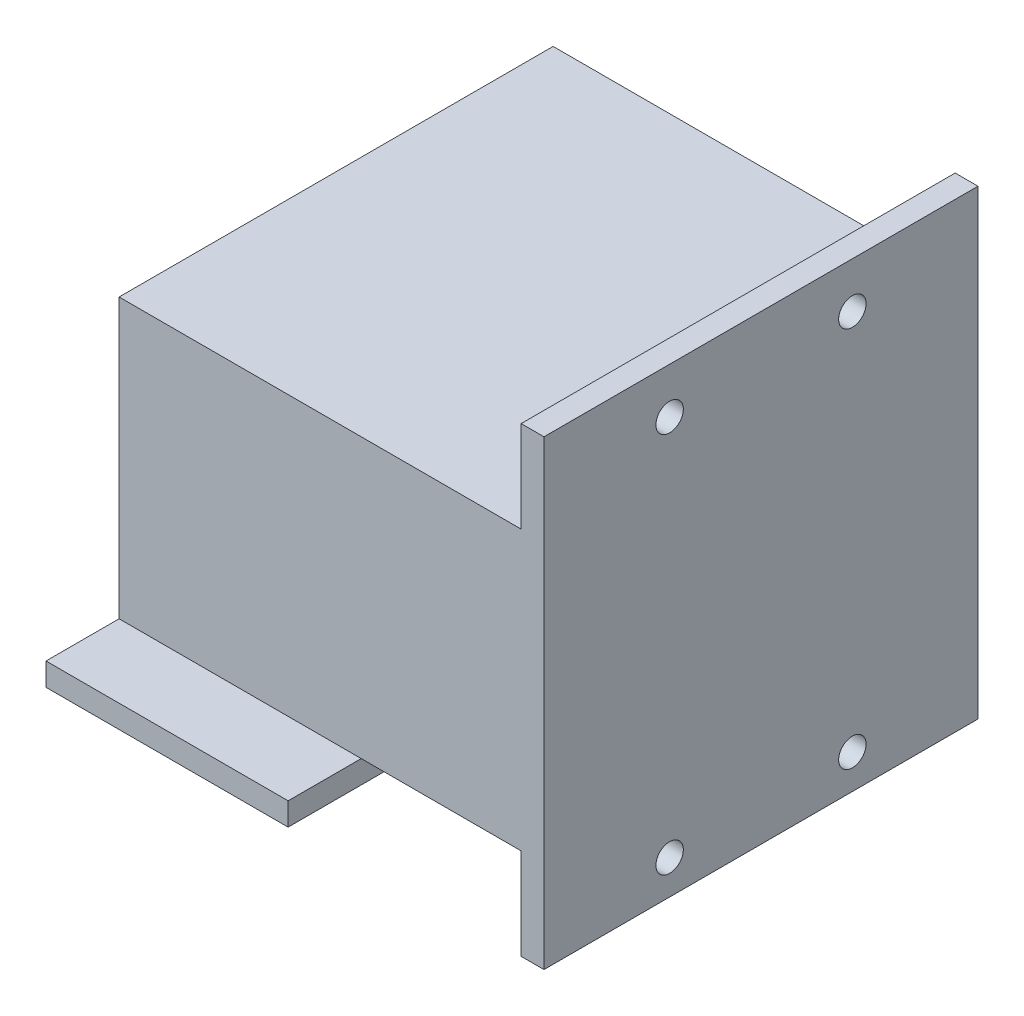
SolidWorks part; units mm, degrees
ref_plane "Front Plane" through (0, 0, 0) normal (0, 0, 1) x (1, 0, 0)
ref_plane "Top Plane" through (0, 0, 0) normal (0, 1, 0) x (1, 0, 0)
ref_plane "Right Plane" through (0, 0, 0) normal (1, 0, 0) x (0, 0, -1)
sketch "Sketch1" plane through (0, 0, 0) normal (0, 1, 0) x (1, 0, 0)
  line L0 (-9.7936, -23.704) -> (11.7064, -23.704)
  line L1 (-9.7936, -23.704) -> (-9.7936, 18.796)
  line L2 (-9.7936, 18.796) -> (11.7064, 18.796)
  line L3 (11.7064, -23.704) -> (11.7064, 18.796)
  line L5 (-12.2936, 21.296) -> (14.2064, 21.296)
  line L6 (-12.2936, 21.296) -> (-12.2936, -26.204)
  line L7 (-12.2936, -26.204) -> (14.2064, -26.204)
  line L8 (14.2064, 21.296) -> (14.2064, -26.204)
  dimension "D1" = 21.5
  dimension "D2" = 42.5
  dimension "D3" = 2.5
  dimension "D4" = 2.5
  dimension "D5" = 2.5
  dimension "D6" = 2.5
extrude "Boss-Extrude1" add sketch "Sketch1" along normal blind 33
sketch "Sketch2" plane through (0, 33, 0) normal (0, 1, 0) x (1, 0, 0)
  line L1 (-9.7936, 18.796) -> (11.7064, 18.796)
  line L2 (-9.7936, 18.796) -> (-9.7936, -23.704)
  line L3 (-9.7936, -23.704) -> (11.7064, -23.704)
  line L4 (11.7064, 18.796) -> (11.7064, -23.704)
extrude "Boss-Extrude2" add sketch "Sketch2" against normal blind 2.5
sketch "Sketch3" plane through (0, 0, -21.296) normal (0, 0, -1) x (-1, 0, 0)
  line L0 (-0.9564, 33) -> (-0.9564, 0) construction
  line L1 (-14.2064, 33) -> (12.2936, 33) construction
  line L2 (-14.2064, 0) -> (12.2936, 0) construction
  line L3 (2.5436, 30.5) -> (2.5436, 0)
  line L4 (2.5436, 0) -> (-0.9564, 0)
  line L5 (-0.9564, 0) -> (-4.4564, 0)
  line L6 (-4.4564, 0) -> (-4.4564, 30.5)
  line L9 (-4.4564, 30.5) -> (2.5436, 30.5)
  dimension "D1" = 3.5
  dimension "D2" = 3.5
  dimension "D3" = 2.5
extrude "Cut-Extrude2" cut sketch "Sketch3" against normal blind 2.5
sketch "Sketch4" plane through (0, 0, 0) normal (0, -1, 0) x (1, 0, 0)
  line L0 (-12.2936, -21.296) -> (-12.2936, -29.296)
  line L1 (-12.2936, 26.204) -> (14.2064, 26.204)
  line L2 (-12.2936, 26.204) -> (-12.2936, 34.204)
  line L3 (-12.2936, 34.204) -> (14.2064, 34.204)
  line L4 (14.2064, 26.204) -> (14.2064, 34.204)
  line L5 (-12.2936, -29.296) -> (-2.5436, -29.296)
  line L6 (-2.5436, -29.296) -> (-2.5436, -21.296)
  line L7 (-2.5436, -21.296) -> (-12.2936, -21.296)
  line L9 (4.4564, -21.296) -> (14.2064, -21.296)
  line L10 (4.4564, -21.296) -> (4.4564, -29.296)
  line L11 (4.4564, -29.296) -> (14.2064, -29.296)
  line L12 (14.2064, -21.296) -> (14.2064, -29.296)
  dimension "D1" = 8
  dimension "D2" = 8
  dimension "D3" = 8
extrude "Boss-Extrude3" add sketch "Sketch4" against normal blind 2.5
sketch "Sketch7" plane through (14.2064, 0, 0) normal (1, 0, 0) x (0, 0, -1)
  line L1 (-26.204, 33) -> (21.296, 33)
  line L2 (-26.204, 33) -> (-26.204, 2.5)
  line L3 (-26.204, 2.5) -> (21.296, 2.5)
  line L4 (21.296, 33) -> (21.296, 2.5)
extrude "Boss-Extrude5" add sketch "Sketch7" along normal blind 20
sketch "Sketch8" plane through (34.2064, 0, 0) normal (1, 0, 0) x (0, 0, -1)
  line L1 (-26.204, 33) -> (21.296, 33)
  line L2 (-26.204, 33) -> (-26.204, 43)
  line L3 (-26.204, 43) -> (21.296, 43)
  line L4 (21.296, 33) -> (21.296, 43)
  line L5 (-26.204, 2.5) -> (21.296, 2.5)
  line L6 (-26.204, 2.5) -> (-26.204, -7.5)
  line L7 (-26.204, -7.5) -> (21.296, -7.5)
  line L8 (21.296, 2.5) -> (21.296, -7.5)
  dimension "D1" = 10
  dimension "D2" = 10
extrude "Boss-Extrude6" add sketch "Sketch8" against normal blind 2.5
sketch "Sketch9" plane through (31.7064, 0, 0) normal (-1, 0, 0) x (0, 0, 1)
  line L0 (2.454, 0) -> (2.454, -7.5) construction
  line L1 (-29.296, 0) -> (34.204, 0) construction
  line L2 (26.204, -7.5) -> (-21.296, -7.5) construction
  line L3 (2.454, 33) -> (2.454, 43) construction
  line L4 (26.204, 33) -> (-21.296, 33) construction
  line L5 (-21.296, 43) -> (26.204, 43) construction
  line L6 (-21.296, 38) -> (26.204, 38) construction
  line L7 (-21.296, 33) -> (-21.296, 43) construction
  line L8 (26.204, 43) -> (26.204, 33) construction
  line L9 (-21.296, 0) -> (-21.296, -7.5) construction
  line L10 (-21.296, -7.5) -> (-21.296, 2.5) construction
  line L11 (-21.296, -3.75) -> (26.204, -3.75) construction
  line L12 (26.204, 2.5) -> (26.204, -7.5) construction
  circle A0 centre (-7.546, -3.75) radius 1.5
  circle A1 centre (12.454, -3.75) radius 1.5
  circle A2 centre (-7.546, 38) radius 1.5
  circle A3 centre (12.454, 38) radius 1.5
  dimension "D5" = 3
  dimension "D6" = 3
  dimension "D7" = 3
  dimension "D8" = 3
  dimension "D1" = 10
  dimension "D2" = 10
  dimension "D3" = 10
  dimension "D4" = 10
extrude "Cut-Extrude3" cut sketch "Sketch9" against normal blind 21.5
